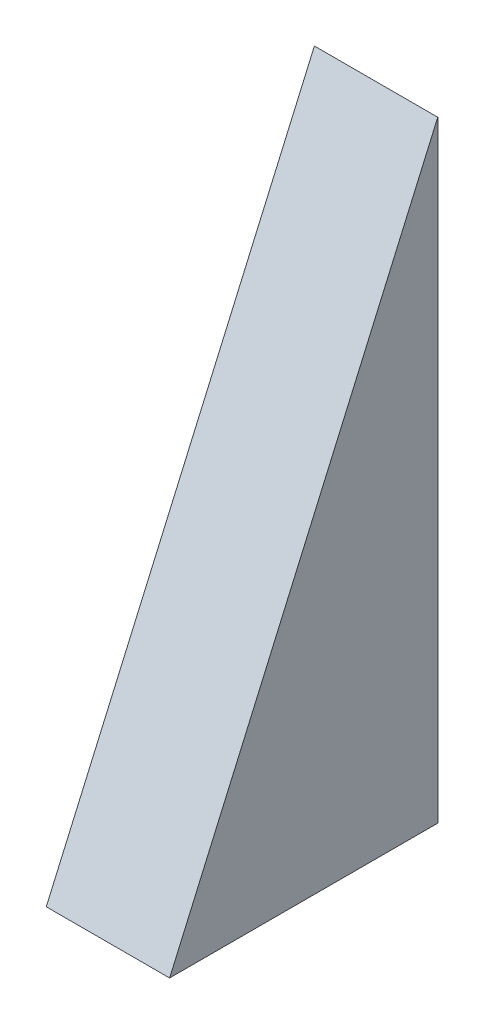
SolidWorks part; units mm, degrees
ref_plane "Front Plane" through (0, 0, 0) normal (0, 0, 1) x (1, 0, 0)
ref_plane "Top Plane" through (0, 0, 0) normal (0, 1, 0) x (1, 0, 0)
ref_plane "Right Plane" through (0, 0, 0) normal (1, 0, 0) x (0, 0, -1)
sketch "Sketch1" plane through (0, 0, 0) normal (1, 0, 0) x (0, 0, -1)
  line L0 (0, 113.0575) -> (0, -74.0554) construction
  line L1 (-169.3132, -24.0554) -> (245.4074, -24.0554) construction
  line L2 (-90, -24.0554) -> (-40, -24.0554)
  line L3 (-40, -24.0554) -> (-40, 89.9446)
  line L4 (-40, 89.9446) -> (-90, -24.0554)
  dimension "D1" = 50
  dimension "D2" = 40
  dimension "D3" = 114
  dimension "D4" = 50
extrude "Boss-Extrude1" add sketch "Sketch1" along normal blind 23
